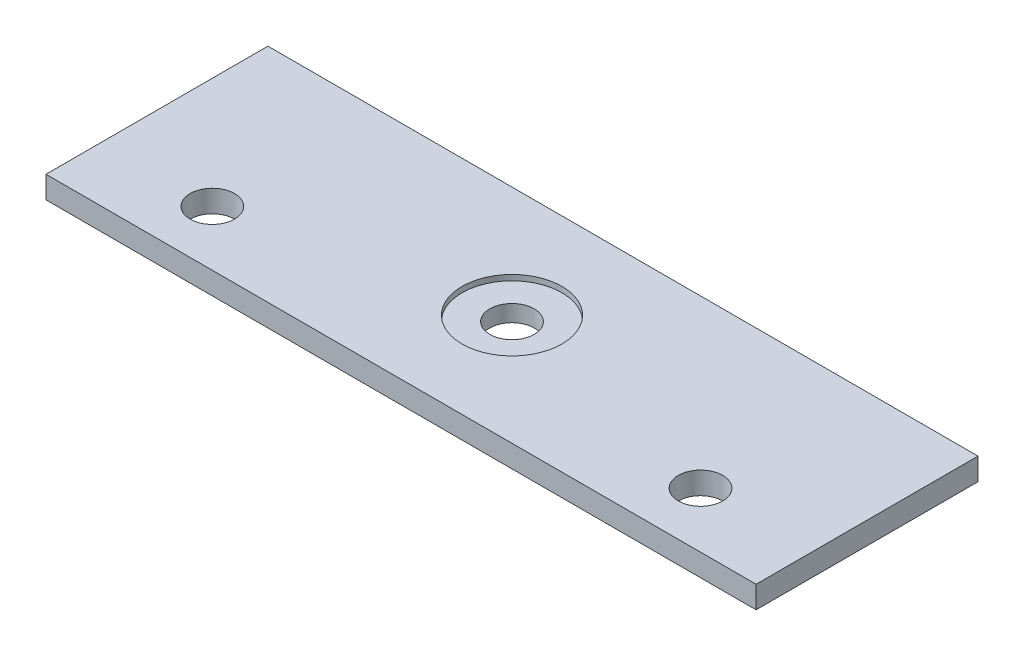
SolidWorks part; units mm, degrees
material "6061 Alloy"
ref_plane "Front" through (0, 0, 0) normal (0, 0, 1) x (1, 0, 0)
ref_plane "Top" through (0, 0, 0) normal (0, 1, 0) x (1, 0, 0)
ref_plane "Right" through (0, 0, 0) normal (1, 0, 0) x (0, 0, -1)
sketch "Sketch8" plane through (0, 0, 0) normal (0, 1, 0) x (1, 0, 0)
  line L0 (-101.6, 63.5) -> (-101.6, 0) construction
  line L1 (0, 0) -> (-203.2, 0)
  line L2 (0, 0) -> (0, 63.5)
  line L3 (0, 63.5) -> (-203.2, 63.5)
  line L4 (-203.2, 0) -> (-203.2, 63.5)
  dimension "D1" = 63.5
  dimension "D2" = 203.2
extrude "Boss-Extrude1" add sketch "Sketch8" along normal blind 6.35
sketch "Sketch9" plane through (0, 6.35, 0) normal (0, 1, 0) x (1, 0, 0)
  line L0 (-101.6, 63.5) -> (-101.6, 0) construction
  line L1 (0, 63.5) -> (-203.2, 63.5) construction
  line L2 (-203.2, 0) -> (0, 0) construction
  circle A0 centre (-101.6, 31.75) radius 14.2875
  dimension "D1" = 28.575
extrude "Cut-Extrude2" cut sketch "Sketch9" against normal blind 1.5875
sketch "Sketch10" plane through (0, 4.7625, 0) normal (0, 1, 0) x (1, 0, 0)
  circle A0 centre (-101.6, 31.75) radius 6.35
  dimension "D1" = 12.7
extrude "Cut-Extrude3" cut sketch "Sketch10" against normal through all
sketch "Sketch11" plane through (0, 6.35, 0) normal (0, 1, 0) x (1, 0, 0)
  line L0 (0, 63.5) -> (-203.2, 63.5) construction
  line L1 (-203.2, 63.5) -> (-203.2, 0) construction
  line L2 (0, 0) -> (0, 63.5) construction
  circle A0 centre (-171.45, 15.85) radius 6.35
  circle A1 centre (-31.75, 15.85) radius 6.35
  dimension "D1" = 12.7
  dimension "D3" = 12.7
  dimension "D2" = 31.75
  dimension "D4" = 31.75
  dimension "D5" = 47.65
extrude "Cut-Extrude4" cut sketch "Sketch11" against normal through all
